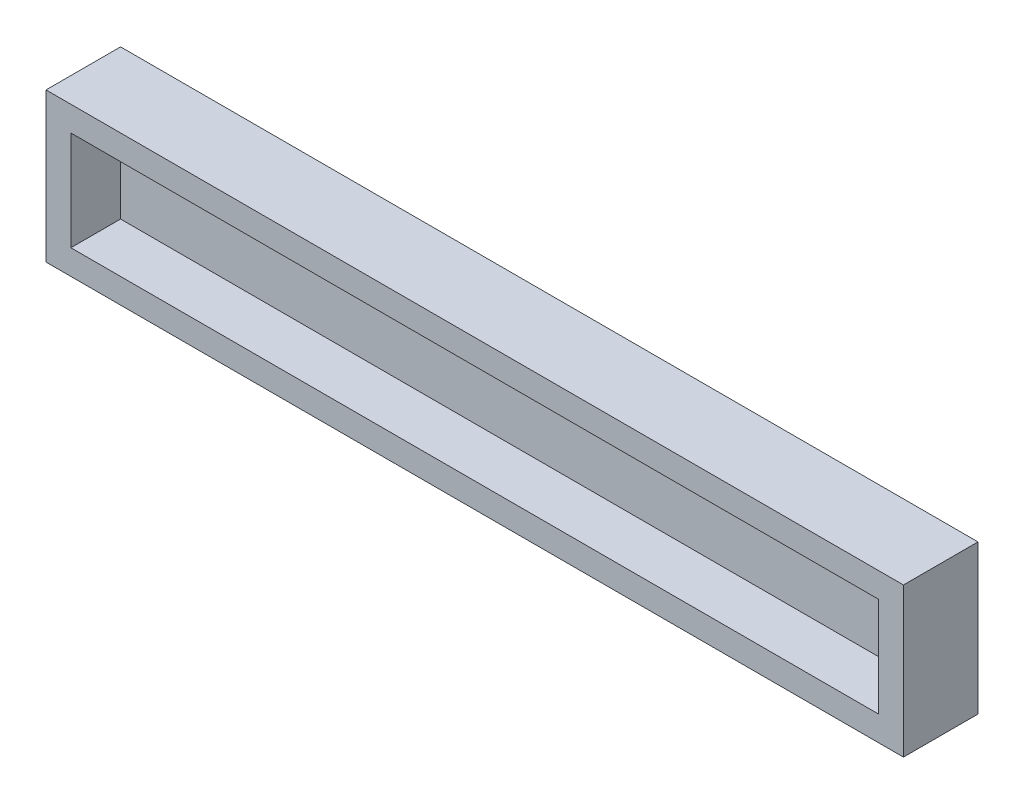
SolidWorks part; units mm, degrees
ref_plane "Front Plane" through (0, 0, 0) normal (0, 0, 1) x (1, 0, 0)
ref_plane "Top Plane" through (0, 0, 0) normal (0, 1, 0) x (1, 0, 0)
ref_plane "Right Plane" through (0, 0, 0) normal (1, 0, 0) x (0, 0, -1)
sketch "Sketch1" plane through (0, 0, 0) normal (0, 0, 1) x (1, 0, 0)
  line L1 (0, 0) -> (97.5, 0)
  line L2 (0, 0) -> (0, 12)
  line L3 (0, 12) -> (97.5, 12)
  line L4 (97.5, 0) -> (97.5, 12)
  dimension "D1" = 12
  dimension "D2" = 97.5
extrude "Boss-Extrude1" add sketch "Sketch1" along normal blind 3
sketch "Sketch2" plane through (0, 0, 0) normal (0, 0, -1) x (-1, 0, 0)
  line L0 (3, -3) -> (-100.5, -3)
  line L1 (0, 0) -> (-97.5, 0)
  line L2 (0, 0) -> (0, 12)
  line L3 (0, 12) -> (-97.5, 12)
  line L4 (-97.5, 0) -> (-97.5, 12)
  line L5 (-100.5, -3) -> (-100.5, 15)
  line L6 (3, 15) -> (-100.5, 15)
  line L7 (3, -3) -> (3, 15)
  dimension "D1" = 3
extrude "Boss-Extrude2" add sketch "Sketch2" against normal offset from surface (9 mm away) 6 up to face at (48.75, 6, 3) offset beyond the face yes
